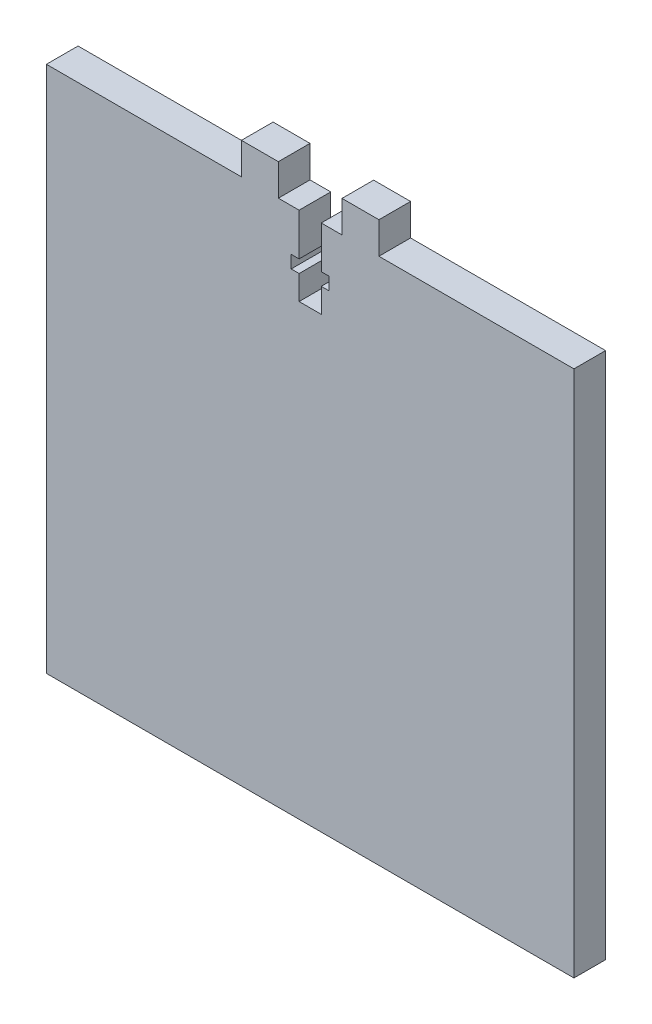
SolidWorks part; units mm, degrees
material "Клен"
ref_plane "Спереди" through (0, 0, 0) normal (0, 0, 1) x (1, 0, 0)
ref_plane "Сверху" through (0, 0, 0) normal (0, 1, 0) x (1, 0, 0)
ref_plane "Справа" through (0, 0, 0) normal (1, 0, 0) x (0, 0, -1)
sketch "Эскиз1" plane through (0, 0, 0) normal (0, 0, 1) x (1, 0, 0)
  line L1 (-50, -50) -> (50, -50)
  line L2 (-50, -50) -> (-50, 50)
  line L3 (-50, 50) -> (50, 50)
  line L4 (50, -50) -> (50, 50)
  line L5 (-50, -50) -> (50, 50) construction
  line L6 (-50, 50) -> (50, -50) construction
  point P0 (0, 0)
  dimension "D1" = 100
extrude "Бобышка-Вытянуть1" add sketch "Эскиз1" along normal blind 6
ref_plane "Плоскость1" through (0, 0, 3) normal (0, 0, 1) x (1, 0, 0)
sketch "Эскиз2" plane through (0, 0, 6) normal (0, 0, 1) x (1, 0, 0)
  line L0 (50, 50) -> (-50, 50) construction
  line L1 (-13.0318, 50) -> (-6.0318, 50)
  line L2 (-13.0318, 50) -> (-13.0318, 56)
  line L3 (-13.0318, 56) -> (-6.0318, 56)
  line L4 (-6.0318, 50) -> (-6.0318, 56)
  line L5 (13, 56) -> (-13, 56) construction
  line L6 (0, 53.4074) -> (0, -162.0434) construction
  line L7 (13.0318, 50) -> (6.0318, 50)
  line L8 (6.0318, 50) -> (6.0318, 56)
  line L9 (13.0318, 56) -> (6.0318, 56)
  line L10 (13.0318, 50) -> (13.0318, 56)
  dimension "D1" = 7
extrude "Бобышка-Вытянуть2" add sketch "Эскиз2" against normal blind 6
sketch "Эскиз3" plane through (0, 0, 6) normal (0, 0, 1) x (1, 0, 0)
  line L1 (6.0318, 50) -> (-6.0318, 50) construction
  line L3 (-2.1, 42) -> (-3.6, 42)
  line L4 (-3.6, 42) -> (-3.6, 39.6)
  line L5 (-3.6, 39.6) -> (-2.1, 39.6)
  line L8 (0, 53.4074) -> (0, -162.0434) construction
  line L11 (3.6, 39.6) -> (2.1, 39.6)
  line L12 (3.6, 42) -> (3.6, 39.6)
  line L13 (2.1, 42) -> (3.6, 42)
  line L16 (-2.1, 42) -> (-2.1, 50)
  line L17 (-2.1, 50) -> (2.1, 50)
  line L18 (2.1, 50) -> (2.1, 42)
  line L19 (2.1, 39.6) -> (2.1, 35)
  line L20 (2.1, 35) -> (-2.1, 35)
  line L21 (-2.1, 35) -> (-2.1, 39.6)
  line L23 (-13.0318, 50) -> (-50, 50) construction
  point P15 (0, 43.65)
  point P20 (0, 50)
  dimension "D1" = 8
  dimension "D2" = 7.2
  dimension "D3" = 2.4
  dimension "D4" = 4.2
  dimension "D5" = 15
extrude "Вырез-Вытянуть1" cut sketch "Эскиз3" against normal through all
